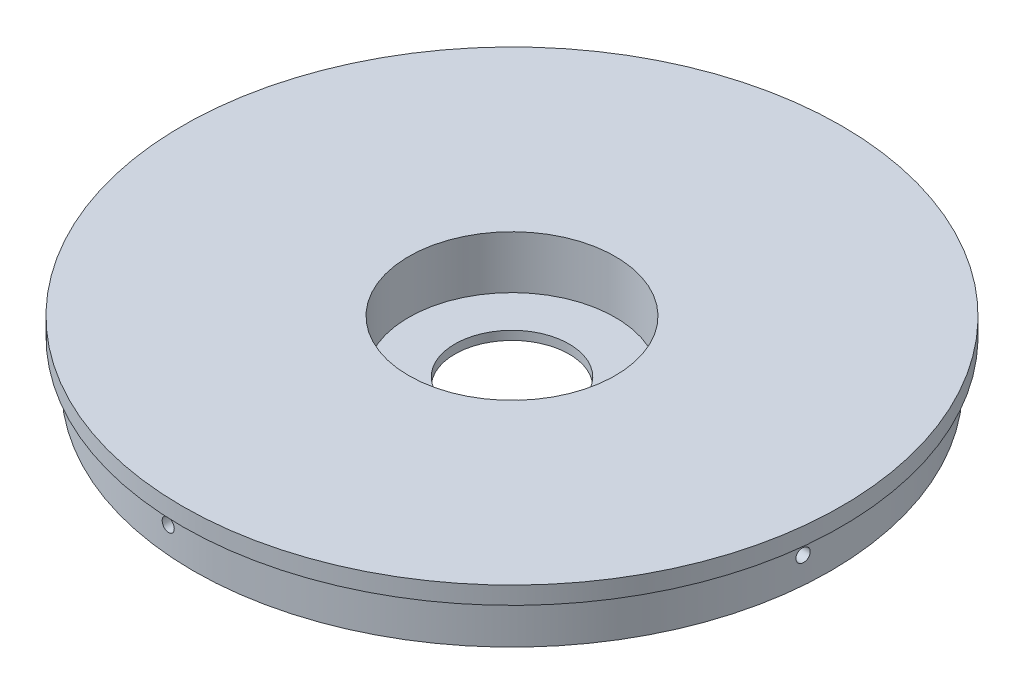
SolidWorks part; units mm, degrees
ref_plane "Płaszczyzna przednia" through (0, 0, 0) normal (0, 0, 1) x (1, 0, 0)
ref_plane "Płaszczyzna górna" through (0, 0, 0) normal (0, 1, 0) x (1, 0, 0)
ref_plane "Płaszczyzna prawa" through (0, 0, 0) normal (1, 0, 0) x (0, 0, -1)
sketch "Szkic4" plane through (0, 0, 0) normal (0, 1, 0) x (1, 0, 0)
  circle A0 centre (0, 0) radius 75
extrude "Dodanie-wyciągnięcie2" add sketch "Szkic4" along normal blind 14
sketch "Szkic5" plane through (0, 14, 0) normal (0, 1, 0) x (1, 0, 0)
  circle A0 centre (0, 0) radius 23.5
extrude "Wytnij-wyciągnięcie3" cut sketch "Szkic5" against normal blind 12
sketch "Szkic6" plane through (0, 2, 0) normal (0, 1, 0) x (1, 0, 0)
  circle A0 centre (0, 0) radius 13
  dimension "D1" = 26
extrude "Wytnij-wyciągnięcie4" cut sketch "Szkic6" against normal blind 12
sketch "Szkic7" plane through (0, 0, 0) normal (0, -1, 0) x (1, 0, 0)
  circle A0 centre (0, 0) radius 75
  circle A1 centre (0, 0) radius 72.5
  circle A2 centre (0, 0) radius 75 construction
  dimension "D1" = 2.5
extrude "Wytnij-wyciągnięcie5" cut sketch "Szkic7" against normal blind 10
sketch "Szkic8" plane through (0, 0, 0) normal (0, -1, 0) x (-1, 0, 0)
  circle A0 centre (23.0603, -19.5004) radius 1.5
  circle A1 centre (-28.8635, 24.4077) radius 1.5
extrude "Wytnij-wyciągnięcie6" cut sketch "Szkic8" against normal blind 6
sketch "Szkic9" plane through (0, 0, 0) normal (0, -1, 0) x (-1, 0, 0)
  line L0 (-28.8635, 24.4077) -> (23.0603, -19.5004) construction
ref_plane "Płaszczyzna1" through (0, 0, 72.5) normal (0, 0, -1) x (0, -1, 0)
sketch "Szkic10" plane through (0, 0, 72.5) normal (0, 0, -1) x (0, -1, 0)
  line L0 (-10, -72.5) -> (-10, 72.5) construction
  circle A0 centre (-6, 6) radius 1.5
  dimension "D1" = 3
  dimension "D2" = 4
extrude "Wytnij-wyciągnięcie7" cut sketch "Szkic10" along normal blind 6
pattern_circular "Szyk kołowy1" count 4 over 360 about axis through (0, 0, 0) along (0, 1, 0) of "Wytnij-wyciągnięcie7"
